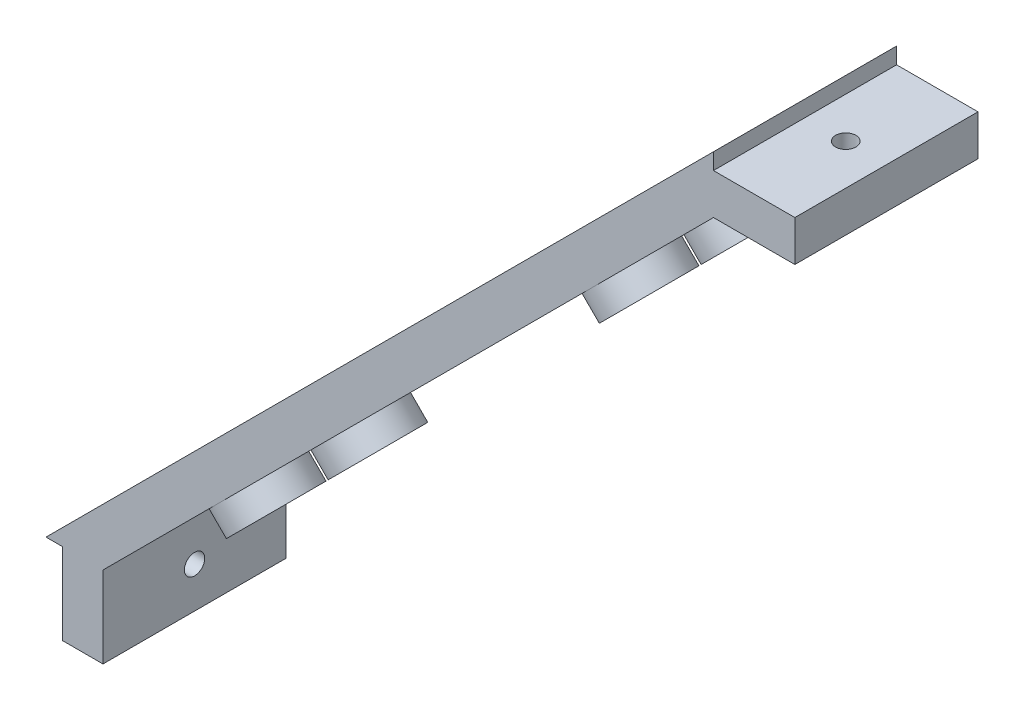
SolidWorks part; units mm, degrees
ref_plane "Front Plane" through (0, 0, 0) normal (0, 0, 1) x (1, 0, 0)
ref_plane "Top Plane" through (0, 0, 0) normal (0, 1, 0) x (1, 0, 0)
ref_plane "Right Plane" through (0, 0, 0) normal (1, 0, 0) x (0, 0, -1)
sketch "Sketch1" plane through (0, 0, 0) normal (0, 0, 1) x (1, 0, 0)
  line L0 (-41, -41) -> (41, 41)
  line L1 (41, 41) -> (41, 39)
  line L2 (-39, -41) -> (-39, -51)
  line L3 (-39, -51) -> (-34, -51)
  line L4 (41, 39) -> (51, 39)
  line L5 (-34, -51) -> (-34, -41)
  line L6 (-41, -41) -> (-39, -41)
  line L7 (-34, -41) -> (41, 34)
  line L8 (41, 34) -> (51, 34)
  line L9 (51, 39) -> (51, 34)
  point P13 (0, 0)
  dimension "D6" = 80
  dimension "D1" = 45
  dimension "D2" = 10
  dimension "D3" = 5
  dimension "D4" = 80
  dimension "D5" = 115.9655
  dimension "D7" = 2
extrude "Main" add sketch "Sketch1" along normal mid plane 22.5
sketch "Sketch2" plane through (41, 0, 0) normal (1, 0, 0) x (0, 0, -1)
  line L0 (11.25, -41) -> (-11.25, -51) construction
  line L1 (-11.25, -41) -> (11.25, -51) construction
  circle A0 centre (0, -46) radius 1.25
  dimension "D1" = 2.5
extrude "FixHole1" cut sketch "Sketch2" against normal through all
sketch "Sketch3" plane through (0, -41, 0) normal (0, -1, 0) x (-1, 0, 0)
  line L4 (-41, 11.25) -> (-51, -11.25) construction
  line L5 (-41, -11.25) -> (-51, 11.25) construction
  circle A1 centre (-46, 0) radius 1.25
  dimension "D1" = 2.5
extrude "FixHole2" cut sketch "Sketch3" against normal through all
sketch "Sketch6" plane through (3.5, -3.5, 0) normal (-0.7071, 0.7071, 0) x (0, 0, 1)
  line L0 (-11.25, 57.9828) -> (-11.25, -57.9828) construction
  circle A0 centre (-6.25, 40) radius 1.25
  dimension "D1" = 2.5
  dimension "D2" = 40
  dimension "D3" = 5
extrude "Cut-Extrude2" cut sketch "Sketch6" along normal through all
pattern_linear "LPattern1" count 5 spacing 20 along (-0.7071, -0.7071, 0) of "Cut-Extrude2"
sketch "Sketch7" plane through (3.5, -3.5, 0) normal (-0.7071, 0.7071, 0) x (0, 0, 1)
  line L0 (-11.25, 57.9828) -> (-11.25, -57.9828) construction
  circle A0 centre (-6.25, -33.0085) radius 5
  circle A1 centre (-6.25, 31.7915) radius 5
  dimension "D1" = 10
  dimension "D2" = 64.8
  dimension "D3" = 32.4
  dimension "D4" = 5
extrude "Boss-Extrude1" add sketch "Sketch7" against normal blind 3
sketch "Sketch8" plane through (5.6213, -5.6213, 0) normal (0.7071, -0.7071, 0) x (0, 0, -1)
  circle A0 centre (6.25, 31.7915) radius 1.25
  circle A1 centre (6.25, 31.7915) radius 5 construction
  circle A2 centre (6.25, -33.0085) radius 1.25
  circle A4 centre (6.25, -33.0085) radius 5 construction
  dimension "D1" = 2.5
extrude "Cut-Extrude3" cut sketch "Sketch8" against normal through all
pattern_linear "LPattern2" count 2 spacing 12.5 along (0, 0, 1) of "LPattern1", "Boss-Extrude1", "Cut-Extrude3", "Cut-Extrude2"
